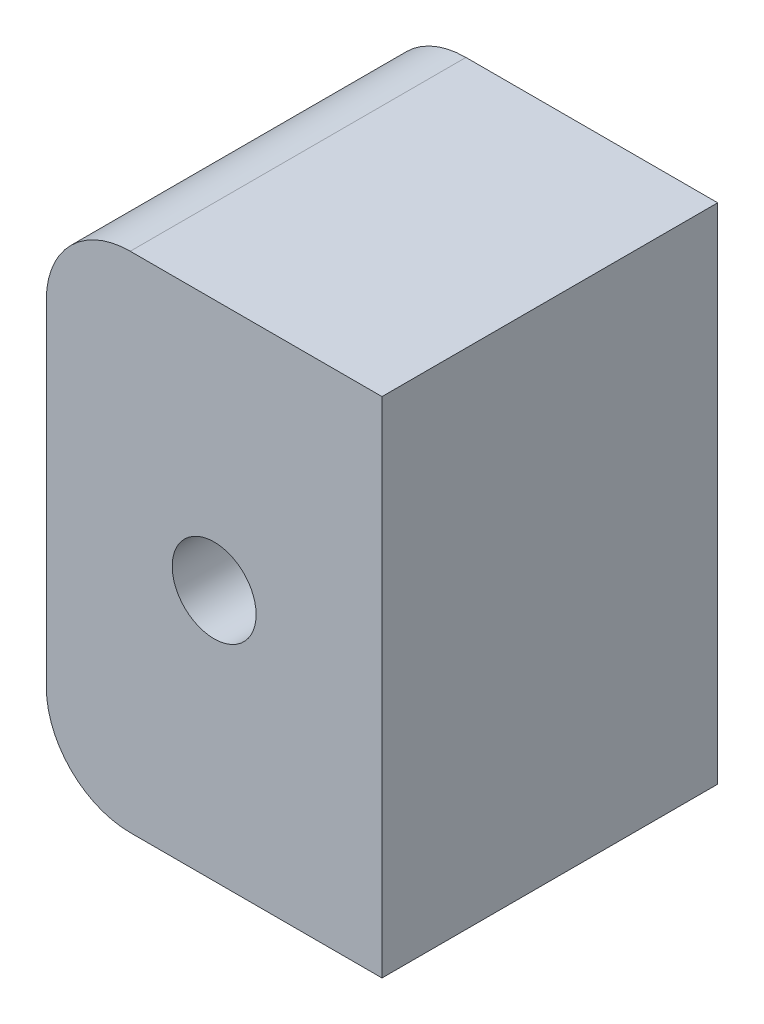
SolidWorks part; units mm, degrees
material "ply"
ref_plane "Front Plane" through (0, 0, 0) normal (0, 0, 1) x (1, 0, 0)
ref_plane "Top Plane" through (0, 0, 0) normal (0, 1, 0) x (1, 0, 0)
ref_plane "Right Plane" through (0, 0, 0) normal (1, 0, 0) x (0, 0, -1)
sketch "Sketch1" plane through (0, 0, 0) normal (0, 0, 1) x (1, 0, 0)
  line L0 (-15, 15) -> (0, 15)
  line L1 (-20, 10) -> (-20, -10)
  line L2 (-15, -15) -> (0, -15)
  line L3 (0, 15) -> (0, -15)
  arc A0 (-20, -10) -> (-15, -15) centre (-15, -10) ccw
  arc A1 (-20, 10) -> (-15, 15) centre (-15, 10) cw
  point P8 (0, 0)
  dimension "D1" = 15
  dimension "D2" = 30
  dimension "D3" = 20
  dimension "D4" = 20
extrude "Boss-Extrude1" add sketch "Sketch1" along normal blind 20
sketch "Sketch2" plane through (0, 0, 20) normal (0, 0, 1) x (1, 0, 0)
  line L0 (0, 0) -> (-20, 0)
  line L1 (-20, 10) -> (-20, -10) construction
  circle A0 centre (-10, 0) radius 2.5
  dimension "D1" = 5
extrude "Cut-Extrude1" cut sketch "Sketch2" against normal through all and the other way through all contours L0 A0 | L0 A0
